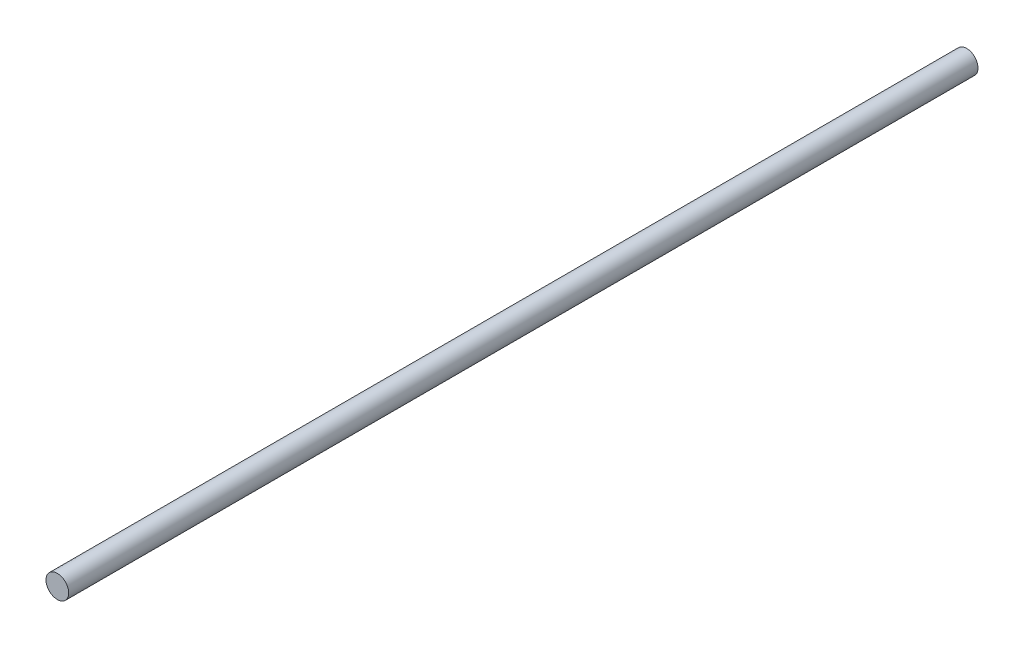
SolidWorks part; units mm, degrees
ref_plane "Plan de face" through (0, 0, 0) normal (0, 0, 1) x (1, 0, 0)
ref_plane "Plan de dessus" through (0, 0, 0) normal (0, 1, 0) x (1, 0, 0)
ref_plane "Plan de droite" through (0, 0, 0) normal (1, 0, 0) x (0, 0, -1)
sketch "Esquisse1" plane through (0, 0, 0) normal (0, 0, 1) x (1, 0, 0)
  circle A0 centre (0, 0) radius 3.75
  dimension "D1" = 7.5
extrude "Boss.-Extru.1" add sketch "Esquisse1" along normal blind 300
